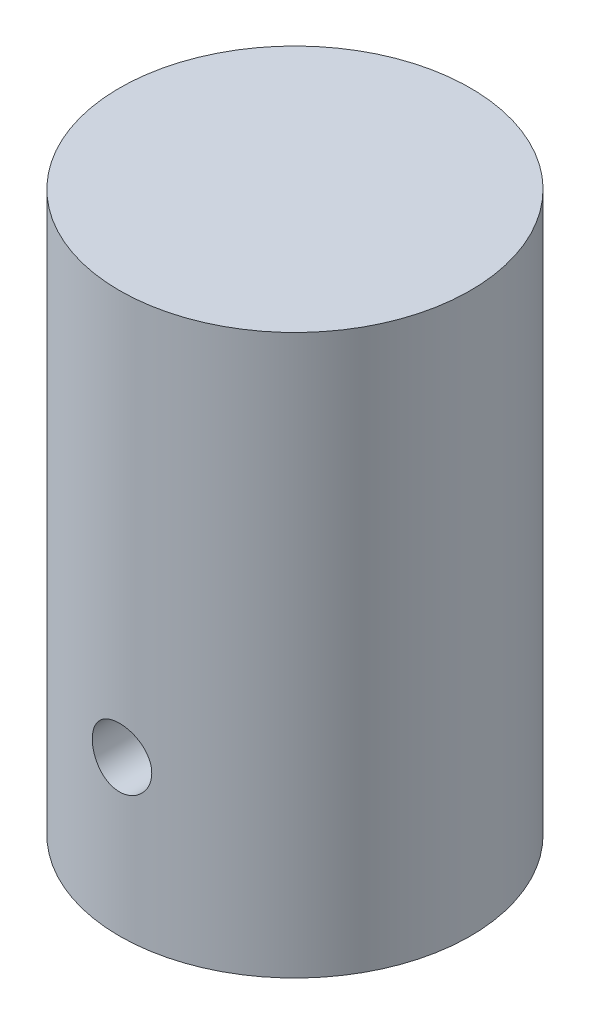
SolidWorks part; units mm, degrees
ref_plane "Front Plane" through (0, 0, 0) normal (0, 0, 1) x (1, 0, 0)
ref_plane "Top Plane" through (0, 0, 0) normal (0, 1, 0) x (1, 0, 0)
ref_plane "Right Plane" through (0, 0, 0) normal (1, 0, 0) x (0, 0, -1)
sketch "Sketch1" plane through (0, 0, 0) normal (0, 1, 0) x (1, 0, 0)
  circle A0 centre (0, 0) radius 37.465
  dimension "D1" = 74.93
extrude "Boss-Extrude1" add sketch "Sketch1" along normal blind 119.38
ref_plane "Plane1" through (0, 0, 37.465) normal (0, 0, 1) x (1, 0, 0)
sketch "Sketch3" plane through (0, 0, 37.465) normal (0, 0, 1) x (1, 0, 0)
  line L0 (0, 0) -> (0, 33.02) construction
  circle A0 centre (0, 33.02) radius 6.35
  dimension "D2" = 12.7
  dimension "D1" = 33.02
extrude "Cut-Extrude1" cut sketch "Sketch3" against normal blind 19.05
sketch "Sketch4" plane through (0, 0, 0) normal (0, -1, 0) x (1, 0, 0)
  circle A0 centre (0, 0) radius 6.35
  dimension "D1" = 12.7
extrude "Cut-Extrude2" cut sketch "Sketch4" against normal blind 19.05
